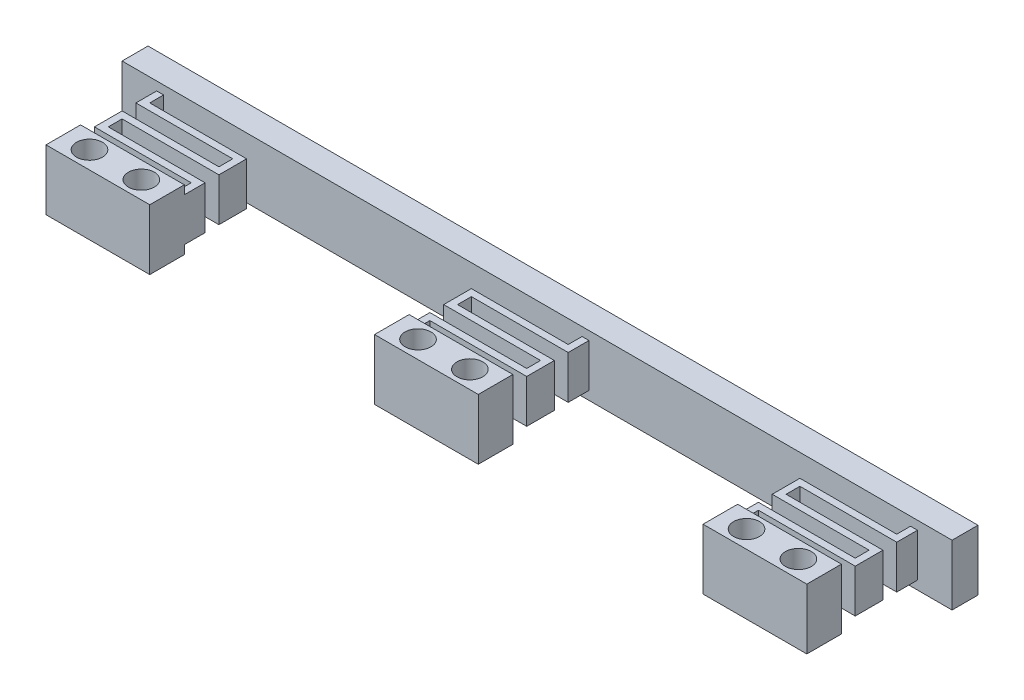
SolidWorks part; units mm, degrees
ref_plane "Front Plane" through (0, 0, 0) normal (0, 0, 1) x (1, 0, 0)
ref_plane "Top Plane" through (0, 0, 0) normal (0, 1, 0) x (1, 0, 0)
ref_plane "Right Plane" through (0, 0, 0) normal (1, 0, 0) x (0, 0, -1)
sketch "스케치1" plane through (0, 0, 0) normal (0, 0, 1) x (1, 0, 0)
  line L0 (0, 0) -> (50000, 0) construction
  line L1 (0, 0) -> (0, 50000) construction
  line L3 (-48, 3.5) -> (48, 3.5)
  line L4 (-48, 3.5) -> (-48, -3.5)
  line L5 (-48, -3.5) -> (48, -3.5)
  line L6 (48, 3.5) -> (48, -3.5)
  dimension "D1" = 96
  dimension "D2" = 7
  dimension "D3" = 3.5
  dimension "D4" = 48
extrude "보스-돌출1" add sketch "스케치1" along normal blind 3
sketch "스케치2" plane through (0, 3.5, 0) normal (0, 1, 0) x (1, 0, 0)
  line L0 (0, 0) -> (0, -50000) construction
  line L1 (-38, -6.0172) -> (-38, -50006.0172) construction
  line L2 (38, -12.0946) -> (38, -50012.0946) construction
  line L3 (-44, -9.0044) -> (-44, -50009.0044) construction
  line L4 (-32, -7.9744) -> (-32, -50007.9744) construction
  line L5 (-6, -9.7255) -> (-6, -50009.7255) construction
  line L6 (6, -13.7427) -> (6, -50013.7427) construction
  line L7 (32, -14.9788) -> (32, -50014.9788) construction
  line L8 (44, -17.348) -> (44, -50017.348) construction
  line L9 (-1056.237, -4.6) -> (48943.763, -4.6) construction
  line L10 (-1056.237, -5.4) -> (48943.763, -5.4) construction
  line L11 (-1056.237, -7) -> (48943.763, -7) construction
  line L12 (-1055.6457, -7.8) -> (48944.3543, -7.8) construction
  line L13 (-1054.8854, -9.4) -> (48945.1146, -9.4) construction
  line L14 (-1054.7165, -10.2) -> (48945.2835, -10.2) construction
  line L15 (-1054.7165, -11.8) -> (48945.2835, -11.8) construction
  line L16 (-1054.1251, -15.8) -> (48945.8749, -15.8) construction
  line L17 (-43.2, -993.6575) -> (-43.2, 49006.3425) construction
  line L18 (-32.8, -993.404) -> (-32.8, 49006.596) construction
  line L19 (-5.2, -995.009) -> (-5.2, 49004.991) construction
  line L20 (5.2, -994.5022) -> (5.2, 49005.4978) construction
  line L21 (32.8, -995.6848) -> (32.8, 49004.3152) construction
  line L22 (43.2, -996.4451) -> (43.2, 49003.5549) construction
  line L23 (48, -3) -> (-48, -3) construction
  line L24 (-44, -3) -> (-44, -5.4)
  line L25 (-44, -5.4) -> (-32.796, -5.4)
  line L26 (-32.796, -5.4) -> (-32.8, -7)
  line L27 (-32.8, -7) -> (-44, -7)
  line L28 (-44, -7) -> (-44, -10.2)
  line L29 (-44, -10.2) -> (-32.8, -10.2)
  line L30 (-32.8, -10.2) -> (-32.8, -11.8)
  line L31 (-32.8, -11.8) -> (-44, -11.8)
  line L32 (-44, -11.8) -> (-44, -15.8)
  line L33 (-44, -15.8) -> (-32, -15.8)
  line L34 (-32, -15.8) -> (-32, -9.4)
  line L35 (-32, -9.4) -> (-43.2, -9.4)
  line L36 (-43.2, -9.4) -> (-43.2, -7.8)
  line L37 (-43.2, -7.8) -> (-32, -7.8)
  line L38 (-32, -7.8) -> (-32, -4.6)
  line L39 (-32, -4.6) -> (-43.2, -4.6)
  line L40 (-43.2, -4.6) -> (-43.2, -3)
  line L41 (-43.2, -3) -> (-44, -3)
  line L42 (44, -3) -> (43.2, -3)
  line L43 (43.2, -3) -> (43.2, -4.6)
  line L44 (43.2, -4.6) -> (32, -4.6)
  line L45 (32, -4.6) -> (32, -7.8)
  line L46 (32, -7.8) -> (43.2, -7.8)
  line L47 (43.2, -7.8) -> (43.2, -9.4)
  line L48 (43.2, -9.4) -> (32, -9.4)
  line L49 (32, -9.4) -> (32, -15.8)
  line L50 (32, -15.8) -> (44, -15.8)
  line L51 (44, -15.8) -> (44, -11.8)
  line L52 (44, -11.8) -> (32.8, -11.8)
  line L53 (32.8, -11.8) -> (32.8, -10.2)
  line L54 (32.8, -10.2) -> (44, -10.2)
  line L55 (44, -10.2) -> (44, -7)
  line L56 (44, -7) -> (32.8, -7)
  line L57 (32.8, -7) -> (32.8, -5.4)
  line L58 (32.8, -5.4) -> (44, -5.4)
  line L59 (44, -5.4) -> (44, -3)
  line L60 (6, -3) -> (5.2, -3)
  line L61 (5.2, -3) -> (5.2, -4.6)
  line L62 (5.2, -4.6) -> (-6, -4.6)
  line L63 (-6, -4.6) -> (-6, -7.8)
  line L64 (-6, -7.8) -> (5.2, -7.8)
  line L65 (5.2, -7.8) -> (5.2, -9.4)
  line L66 (5.2, -9.4) -> (-6, -9.4)
  line L67 (-6, -9.4) -> (-6, -15.8)
  line L68 (-6, -15.8) -> (6, -15.8)
  line L69 (6, -15.8) -> (6, -11.8)
  line L70 (6, -11.8) -> (-5.2, -11.8)
  line L71 (-5.2, -11.8) -> (-5.2, -10.2)
  line L72 (-5.2, -10.2) -> (6, -10.2)
  line L73 (6, -10.2) -> (6, -7)
  line L74 (6, -7) -> (-5.2, -7)
  line L75 (-5.2, -7) -> (-5.2, -5.4)
  line L76 (-5.2, -5.4) -> (6, -5.4)
  line L77 (6, -5.4) -> (6, -3)
  dimension "D1" = 38
  dimension "D2" = 38
  dimension "D3" = 6
  dimension "D4" = 6
  dimension "D5" = 6
  dimension "D6" = 6
  dimension "D7" = 0.8
  dimension "D8" = 0.8
  dimension "D9" = 0.8
  dimension "D10" = 0.8
  dimension "D11" = 0.8
  dimension "D12" = 0.8
  dimension "D13" = 1.6
  dimension "D14" = 0.8
  dimension "D15" = 1.6
  dimension "D16" = 0.8
  dimension "D17" = 1.6
  dimension "D18" = 0.8
  dimension "D19" = 1.6
  dimension "D20" = 4
  dimension "D21" = 6
  dimension "D22" = 6
extrude "보스-돌출2" add sketch "스케치2" against normal blind 7 separate body
sketch "스케치3" plane through (0, 3.5, 0) normal (0, 1, 0) x (1, 0, 0)
  line L0 (-48.001, -13.7714) -> (49951.999, -13.7714) construction
  line L1 (-38, 4.6668) -> (-38, 50004.6668) construction
  line L2 (0, 0) -> (0, -50000) construction
  line L3 (38, 2.9157) -> (38, -49997.0843) construction
  line L4 (-41, -20.4715) -> (-41, 49979.5285) construction
  line L5 (-35, -21.8794) -> (-35, 49978.1206) construction
  line L6 (-3, -23.2873) -> (-3, 49976.7127) construction
  line L7 (3, -19.2044) -> (3, 49980.7956) construction
  line L8 (35, -19.0595) -> (35, 49980.9405) construction
  line L9 (41, -19.3505) -> (41, 49980.6495) construction
  circle A0 centre (-41, -13.7714) radius 1.5
  circle A1 centre (-35, -13.7714) radius 1.5
  circle A2 centre (-3, -13.7714) radius 1.5
  circle A3 centre (3, -13.7714) radius 1.5
  circle A4 centre (35, -13.7714) radius 1.5
  circle A5 centre (41, -13.7714) radius 1.5
  dimension "D1" = 38
  dimension "D2" = 38
  dimension "D3" = 3
  dimension "D4" = 3
  dimension "D5" = 3
  dimension "D6" = 3
  dimension "D7" = 3
  dimension "D8" = 3
extrude "컷-돌출1" cut sketch "스케치3" against normal blind 10
sketch "스케치4" plane through (-48, 0, 0) normal (-1, 0, 0) x (0, 0, 1)
  line L0 (-1.5637, 2.5) -> (49998.4363, 2.5) construction
  line L1 (-2.1193, -2.5) -> (49997.8807, -2.5) construction
  line L2 (3, 0.6431) -> (3, -49999.3569) construction
  line L3 (11.8, 0.7879) -> (11.8, -49999.2121) construction
  line L4 (3, -3.5) -> (3, 3.5) construction
  line L5 (11.8, -3.5) -> (11.8, 3.5) construction
  line L7 (3, -3.5) -> (0, -3.5) construction
  line L8 (3, 2.5) -> (11.8, 2.5)
  line L9 (3, 2.5) -> (3, 4.3258)
  line L10 (3, 4.3258) -> (11.8, 4.3258)
  line L11 (11.8, 2.5) -> (11.8, 4.3258)
  line L12 (11.8, -2.5) -> (3, -2.5)
  line L13 (11.8, -2.5) -> (11.8, -4.1847)
  line L14 (11.8, -4.1847) -> (3, -4.1847)
  line L15 (3, -2.5) -> (3, -4.1847)
  dimension "D1" = 0
  dimension "D2" = 0
  dimension "D3" = 1
extrude "컷-돌출2" cut sketch "스케치4" against normal blind 107
